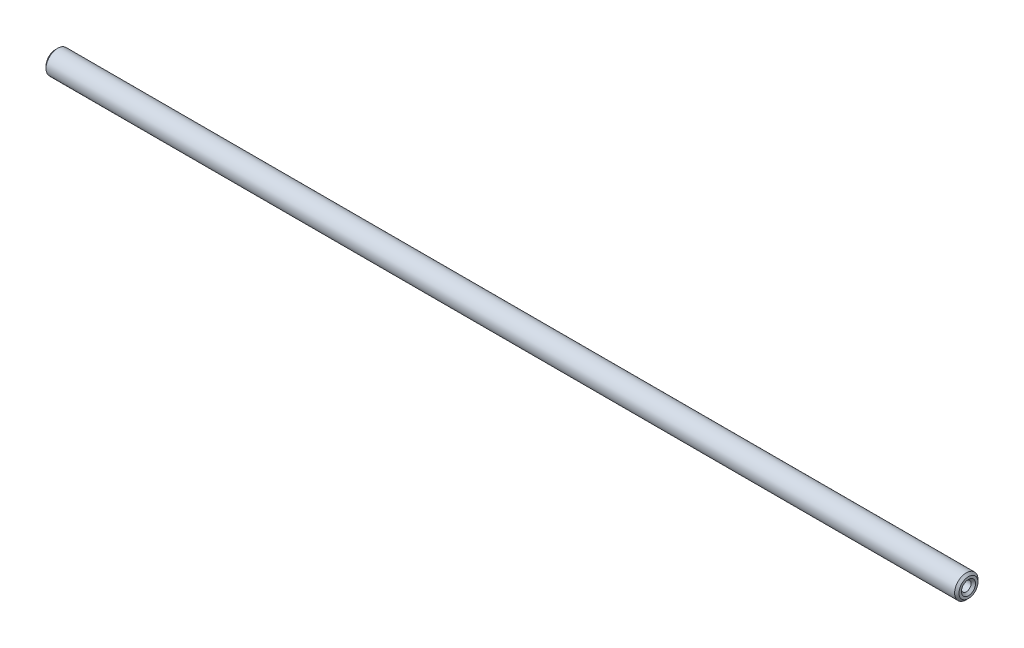
SolidWorks part; units mm, degrees
ref_plane "Face" through (0, 0, 0) normal (0, 0, 1) x (1, 0, 0)
ref_plane "Dessus" through (0, 0, 0) normal (0, 1, 0) x (1, 0, 0)
ref_plane "Droite" through (0, 0, 0) normal (1, 0, 0) x (0, 0, -1)
sketch "Esquisse1" plane through (0, 0, 0) normal (1, 0, 0) x (0, 0, -1)
  circle A0 centre (0, 0) radius 4
  dimension "D1" = 8
extrude "Boss.-Extru.1" add sketch "Esquisse1" along normal mid plane 312
ref_plane "Milieux Axe" through (0, 0, 0) normal (-1, 0, 0) x (0, 0, 1)
sketch "Esquisse2" plane through (-156, 0, 0) normal (-1, 0, 0) x (0, 0, 1)
  circle A0 centre (0, 0) radius 1.65
  dimension "D1" = 3.3
extrude "Enlèv. mat.-Extru.1" cut sketch "Esquisse2" against normal through all
chamfer "Chanfrein1" distance 0.75 angle 45 4 edges at (156, 0, 1.65) (156, 0, -4) (-156, 0, 1.65) (-156, 0, -4)
sketch "Esquisse3" plane through (0, 0, 0) normal (0, 0, 1) x (1, 0, 0)
  line L0 (-155.25, 0) -> (155.25, 0)
  line L1 (-155.25, 4) -> (-155.25, -4) construction
  line L2 (155.25, -4) -> (155.25, 4) construction
